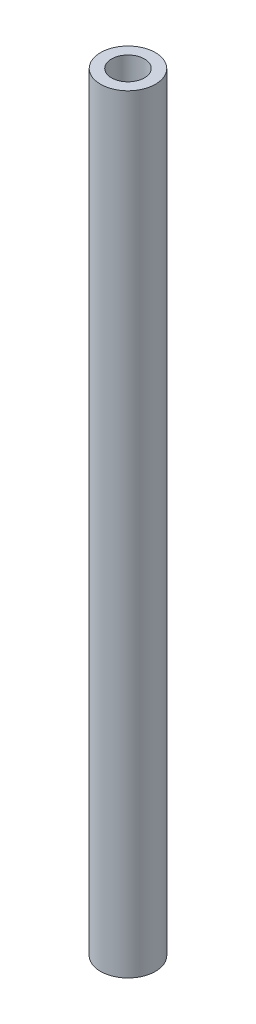
SolidWorks part; units mm, degrees
ref_plane "前视基准面" through (0, 0, 0) normal (0, 0, 1) x (1, 0, 0)
ref_plane "上视基准面" through (0, 0, 0) normal (0, 1, 0) x (1, 0, 0)
ref_plane "右视基准面" through (0, 0, 0) normal (1, 0, 0) x (0, 0, -1)
sketch "草图1" plane through (0, 0, 0) normal (0, 1, 0) x (1, 0, 0)
  circle A0 centre (0, 0) radius 1.5
  circle A1 centre (0, 0) radius 2.5
  dimension "D1" = 3
  dimension "D2" = 5
extrude "凸台-拉伸1" add sketch "草图1" along normal blind 70
